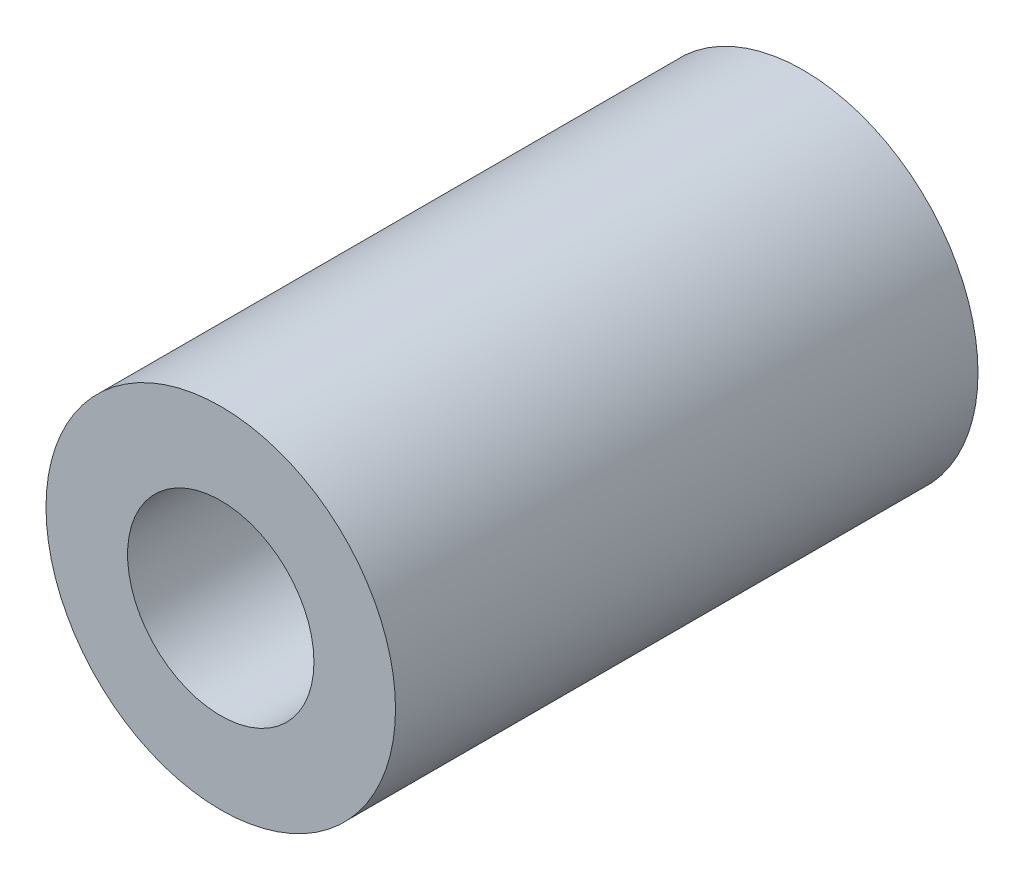
SolidWorks part; units mm, degrees
material "Plain Carbon Steel"
ref_plane "Front Plane" through (0, 0, 0) normal (0, 0, 1) x (1, 0, 0)
ref_plane "Top Plane" through (0, 0, 0) normal (0, 1, 0) x (1, 0, 0)
ref_plane "Right Plane" through (0, 0, 0) normal (1, 0, 0) x (0, 0, -1)
sketch "Sketch1" plane through (0, 0, 0) normal (0, 0, 1) x (1, 0, 0)
  circle A0 centre (0, 0) radius 1.6
  circle A1 centre (0, 0) radius 3
  dimension "D1" = 6
  dimension "D2" = 3.2
extrude "Boss-Extrude1" add sketch "Sketch1" along normal blind 10
